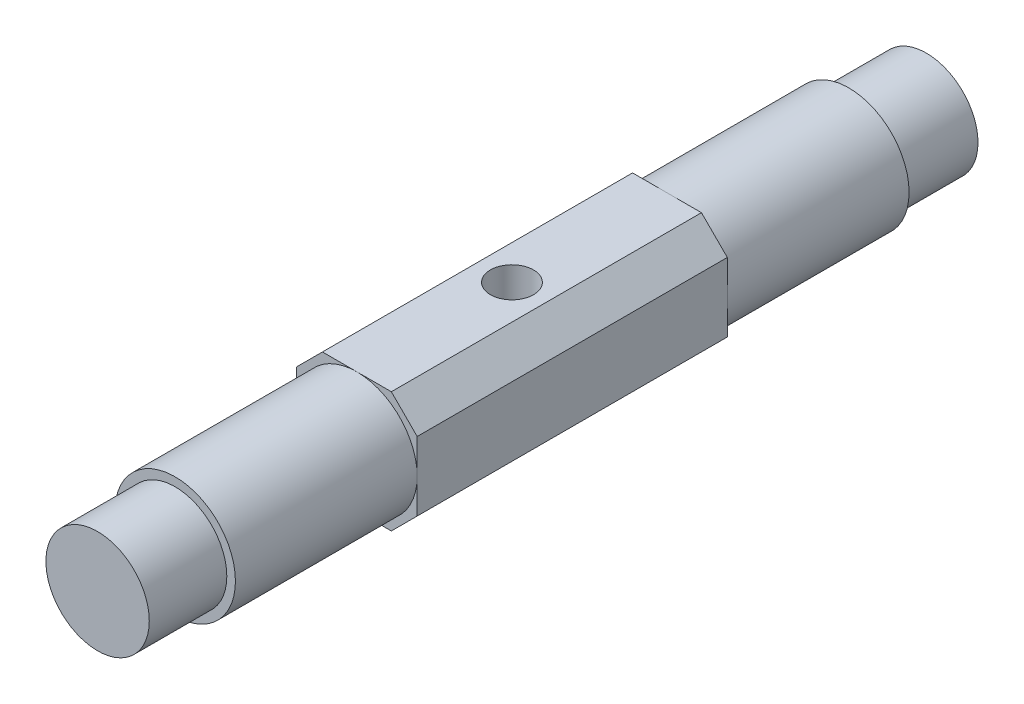
SolidWorks part; units mm, degrees
material "ejes"
ref_plane "Alzado" through (0, 0, 0) normal (0, 0, 1) x (1, 0, 0)
ref_plane "Planta" through (0, 0, 0) normal (0, 1, 0) x (1, 0, 0)
ref_plane "Vista lateral" through (0, 0, 0) normal (1, 0, 0) x (0, 0, -1)
sketch "Croquis1" plane through (0, 0, 0) normal (0, 0, 1) x (1, 0, 0)
  circle A0 centre (0, 0) radius 3
extrude "Saliente-Extruir1" add sketch "Croquis1" along normal blind 4.5
sketch "Croquis2" plane through (0, 0, 4.5) normal (0, 0, 1) x (1, 0, 0)
  circle A0 centre (0, 0) radius 3.5
extrude "Saliente-Extruir2" add sketch "Croquis2" along normal blind 10.55
sketch "Croquis3" plane through (0, 0, 15.05) normal (0, 0, 1) x (1, 0, 0)
  line L1 (3.5, -3.5) -> (-3.5, -3.5)
  line L2 (3.5, -3.5) -> (3.5, 3.5)
  line L3 (3.5, 3.5) -> (-3.5, 3.5)
  line L4 (-3.5, -3.5) -> (-3.5, 3.5)
  line L5 (3.5, -3.5) -> (-3.5, 3.5) construction
  line L6 (3.5, 3.5) -> (-3.5, -3.5) construction
  point P0 (0, 0)
  dimension "D1" = 7
  dimension "D2" = 7
extrude "Saliente-Extruir3" add sketch "Croquis3" along normal blind 18 contours L3 L4 L1 L2
sketch "Croquis4" plane through (0, 0, 33.05) normal (0, 0, 1) x (1, 0, 0)
  circle A0 centre (0, 0) radius 3.5
extrude "Saliente-Extruir4" add sketch "Croquis4" along normal blind 10.55
sketch "Croquis5" plane through (0, 0, 43.6) normal (0, 0, 1) x (1, 0, 0)
  circle A0 centre (0, 0) radius 3
extrude "Saliente-Extruir5" add sketch "Croquis5" along normal blind 4.5
sketch "Croquis6" plane through (0, 3.5, 0) normal (0, 1, 0) x (1, 0, 0)
  circle A0 centre (0, -24.05) radius 1.25
  dimension "D1" = 9
extrude "Cortar-Extruir1" cut sketch "Croquis6" against normal through all
chamfer "Chaflán1" distance 1.5 angle 45 4 edges at (3.5, -3.5, 24.05) (3.5, 3.5, 24.05) (-3.5, -3.5, 24.05) (-3.5, 3.5, 24.05)
